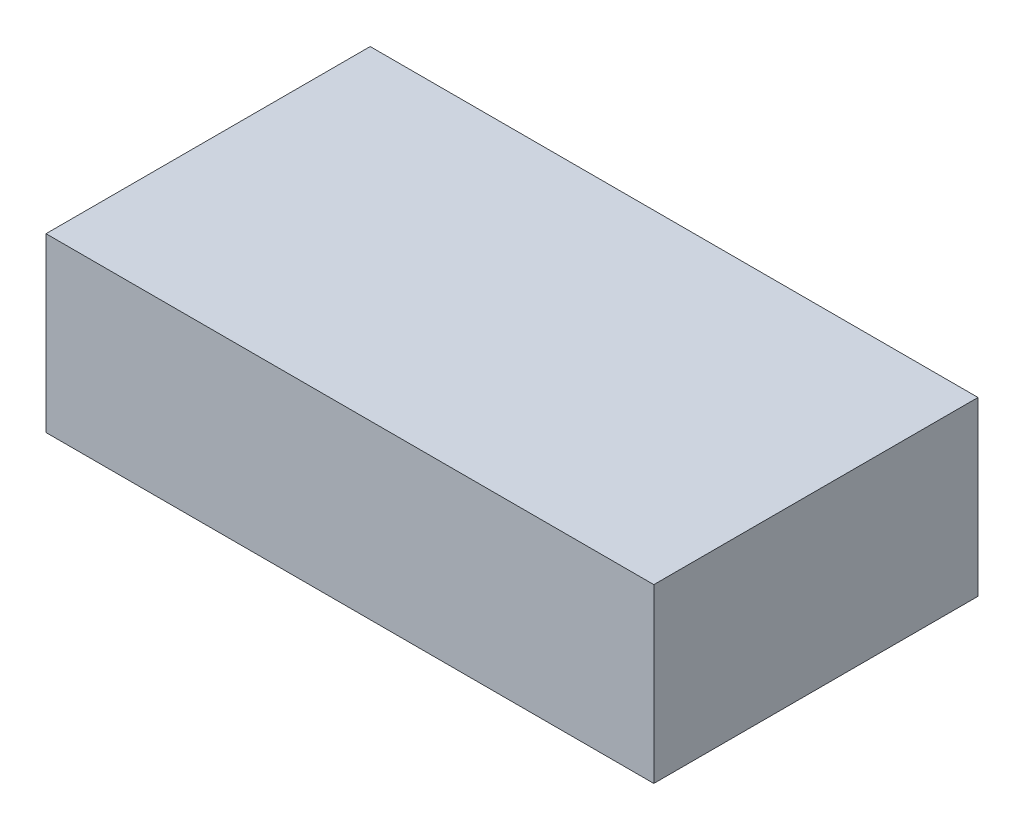
SolidWorks part; units mm, degrees
ref_plane "Front Plane" through (0, 0, 0) normal (0, 0, 1) x (1, 0, 0)
ref_plane "Top Plane" through (0, 0, 0) normal (0, 1, 0) x (1, 0, 0)
ref_plane "Right Plane" through (0, 0, 0) normal (1, 0, 0) x (0, 0, -1)
sketch "Sketch1" plane through (0, 0, 0) normal (0, 1, 0) x (1, 0, 0)
  line L0 (-76.2, -40.64) -> (76.2, 40.64) construction
  line L1 (-76.2, 40.64) -> (76.2, 40.64)
  line L2 (-76.2, 40.64) -> (-76.2, -40.64)
  line L3 (-76.2, -40.64) -> (76.2, -40.64)
  line L4 (76.2, 40.64) -> (76.2, -40.64)
  dimension "D1" = 152.4
  dimension "D2" = 81.28
extrude "Boss-Extrude1" add sketch "Sketch1" along normal mid plane 43.18
